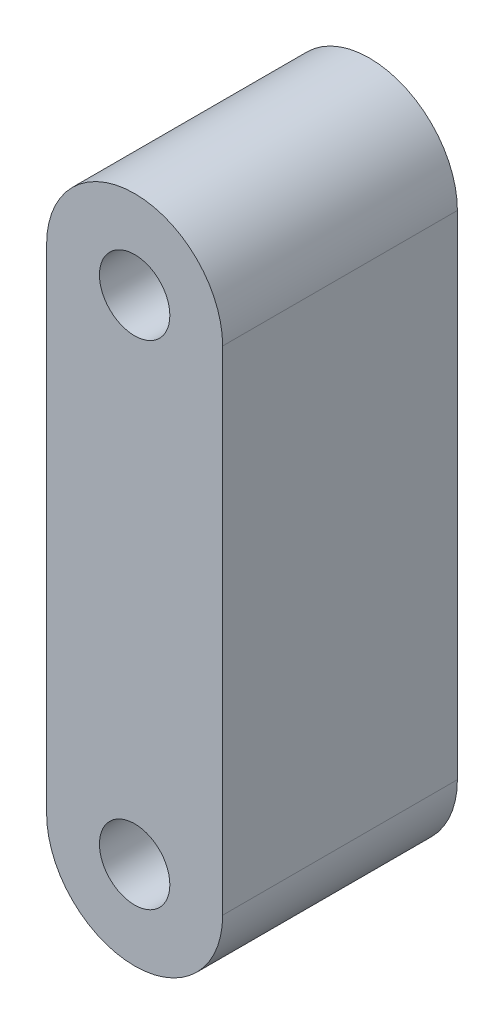
SolidWorks part; units mm, degrees
material "ABS"
ref_plane "Front Plane" through (0, 0, 0) normal (0, 0, 1) x (1, 0, 0)
ref_plane "Top Plane" through (0, 0, 0) normal (0, 1, 0) x (1, 0, 0)
ref_plane "Right Plane" through (0, 0, 0) normal (1, 0, 0) x (0, 0, -1)
sketch "Sketch1" plane through (0, 0, 0) normal (0, 0, 1) x (1, 0, 0)
  line L0 (0, 0) -> (0, 21) construction
  line L1 (-3.75, 0) -> (-3.75, 21)
  line L2 (3.75, 0) -> (3.75, 21)
  arc A0 (-3.75, 0) -> (3.75, 0) centre (0, 0) ccw
  arc A1 (3.75, 21) -> (-3.75, 21) centre (0, 21) ccw
  circle A2 centre (0, 21) radius 1.5
  circle A3 centre (0, 0) radius 1.5
  point P3 (0, 10.5)
  dimension "D1" = 3.75
  dimension "D2" = 3
  dimension "D3" = 21
extrude "Boss-Extrude1" add sketch "Sketch1" along normal blind 10
